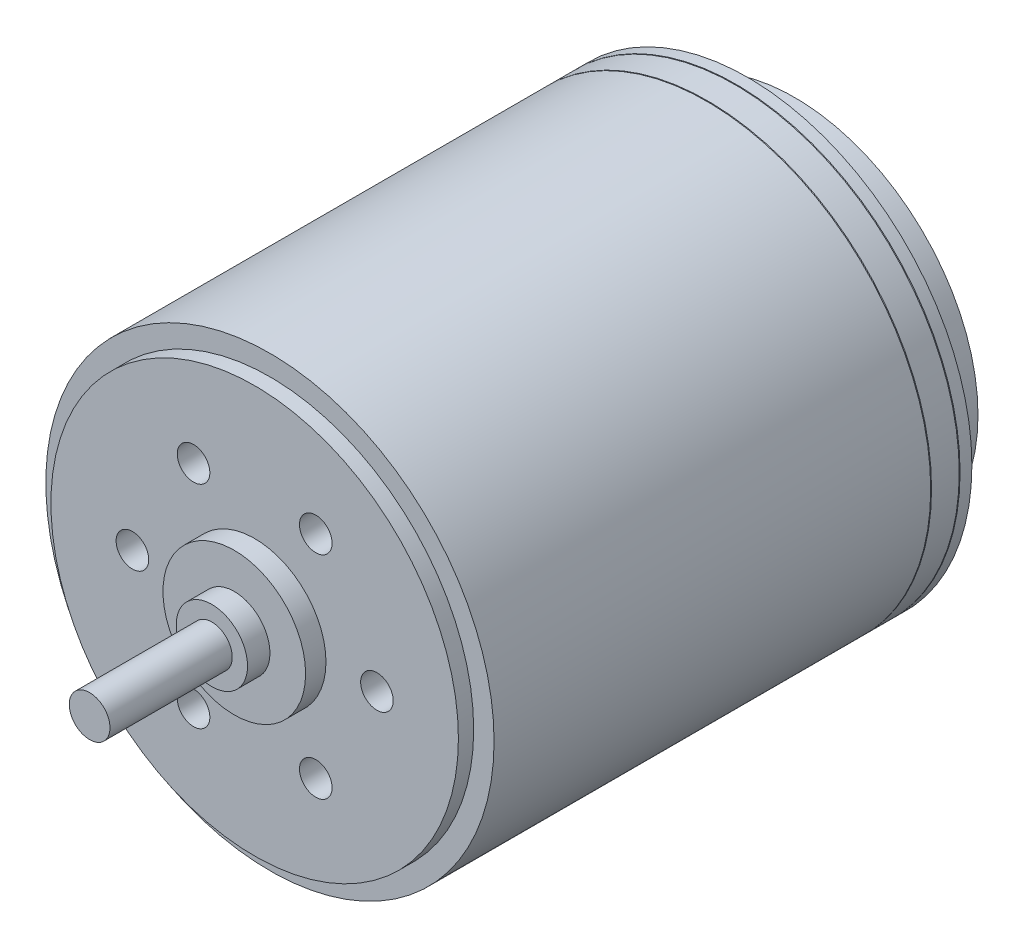
SolidWorks part; units mm, degrees
ref_plane "Front Plane" through (0, 0, 0) normal (0, 0, 1) x (1, 0, 0)
ref_plane "Top Plane" through (0, 0, 0) normal (0, 1, 0) x (1, 0, 0)
ref_plane "Right Plane" through (0, 0, 0) normal (1, 0, 0) x (0, 0, -1)
sketch "Sketch1" plane through (0, 0, 0) normal (0, 1, 0) x (1, 0, 0)
  line L0 (11, 0) -> (0, 0)
  line L1 (0, 0) -> (0, -23.45)
  line L2 (0, -23.45) -> (11, -23.45)
  line L3 (11, -23.45) -> (11, -2.0207)
  line L4 (11, -2.0207) -> (10.95, -2)
  line L5 (10.95, -2) -> (11, -1.9793)
  line L6 (11, -1.9793) -> (11, -0.6207)
  line L7 (11, -0.6207) -> (10.95, -0.6)
  line L8 (10.95, -0.6) -> (11, -0.5793)
  line L9 (11, -0.5793) -> (11, 0)
  line L10 (0, 0) -> (0, -23.45) construction
revolve "Revolve1" add sketch "Sketch1" angle 360 about L10
sketch "Sketch6" plane through (0, 0, 0) normal (0, 0, -1) x (-1, 0, 0)
  line L0 (5.05, 5.4772) -> (5.05, -5.4772)
  line L1 (-5.05, -5.4772) -> (-5.05, 5.4772)
  arc A0 (-5.05, 5.4772) -> (5.05, 5.4772) centre (0, 0) cw
  arc A1 (5.05, -5.4772) -> (-5.05, -5.4772) centre (0, 0) cw
extrude "Boss-Extrude3" add sketch "Sketch6" along normal blind 1
sketch "Sketch7" plane through (0, 0, 23.45) normal (0, 0, 1) x (1, 0, 0)
  circle A0 centre (0, 0) radius 10
extrude "Boss-Extrude4" add sketch "Sketch7" along normal blind 0.75
sketch "Sketch8" plane through (0, 0, 24.2) normal (0, 0, 1) x (1, 0, 0)
  circle A0 centre (0, 0) radius 3.5
extrude "Boss-Extrude5" add sketch "Sketch8" along normal blind 1
sketch "Sketch9" plane through (0, 0, 25.2) normal (0, 0, 1) x (1, 0, 0)
  circle A0 centre (0, 0) radius 1.75
extrude "Boss-Extrude6" add sketch "Sketch9" along normal blind 1.1
sketch "Sketch10" plane through (0, 0, 26.3) normal (0, 0, 1) x (1, 0, 0)
  circle A0 centre (0, 0) radius 1
extrude "Boss-Extrude7" add sketch "Sketch10" along normal blind 6
hole_wizard "Ø1.6 (1.6) Diameter Hole1" positions "Sketch12" profile "Sketch11" hole size "Ø1.6" standard "ANSI Metric"
sketch "Sketch12" plane through (0, 0, 24.2) normal (0, 0, 1) x (1, 0, 0)
  point P0 (-3, 5.1962)
  point P1 (3, 5.1962)
  point P2 (6, 0)
  point P3 (3, -5.1962)
  point P4 (-3, -5.1962)
  point P5 (-6, 0)
sketch "Sketch11" plane through (-3, 5.1962, 24.2) normal (1, 0, 0) x (0, -1, 0)
  line L0 (0, 0) -> (0, 4.9807)
  line L1 (0, 4.9807) -> (0.8, 4.5)
  line L2 (0.8, 4.5) -> (0.8, 0)
  line L5 (0.8, 0) -> (0, 0)
  line L10 (0, 4.9807) -> (-0.8, 4.5) construction
  line L11 (0, -6.35) -> (0, 107.95) construction
  dimension "Hole Dia." = 1.6
  dimension "Hole Depth" = 4.5
  dimension "Drill Angle" = 118
sketch "Sketch13" plane through (0, 0, 0) normal (0, 0, -1) x (-1, 0, 0)
  circle A0 centre (0, 0) radius 9
extrude "Boss-Extrude8" add sketch "Sketch13" along normal blind 2.3
